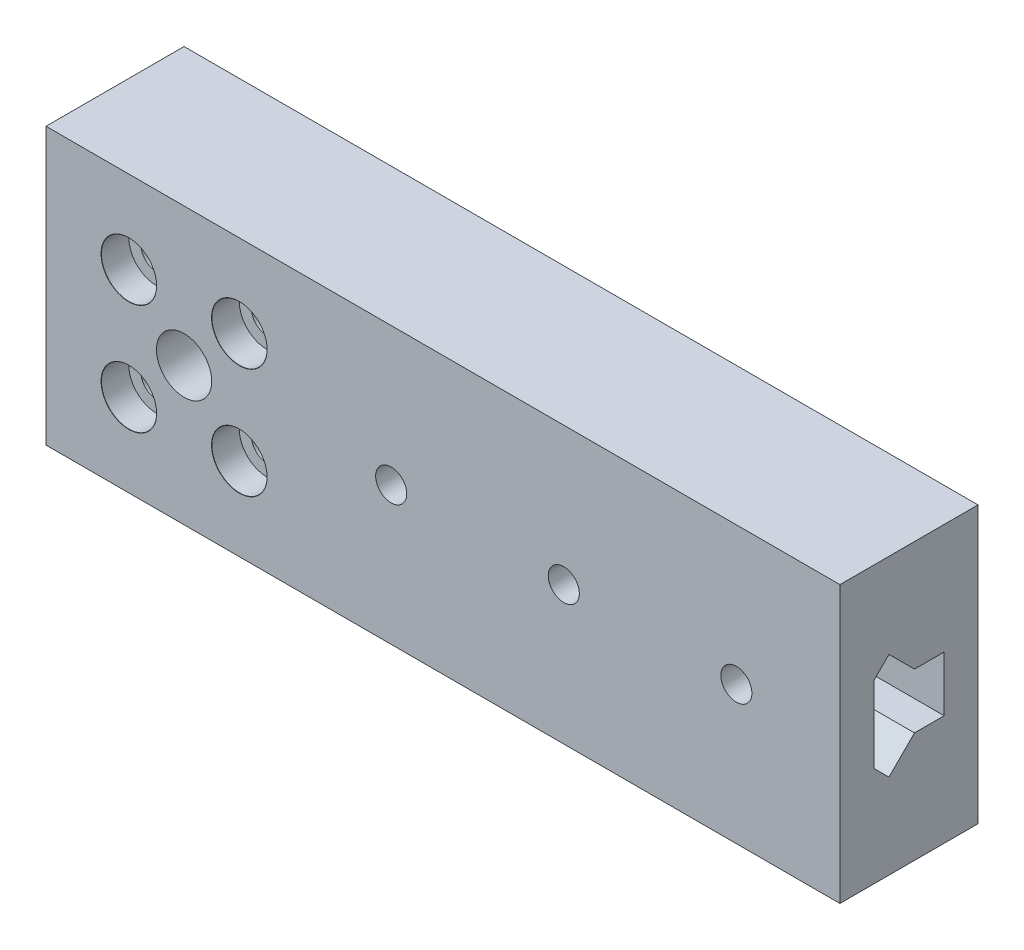
SolidWorks part; units mm, degrees
ref_plane "Front Plane" through (0, 0, 0) normal (0, 0, 1) x (1, 0, 0)
ref_plane "Top Plane" through (0, 0, 0) normal (0, 1, 0) x (1, 0, 0)
ref_plane "Right Plane" through (0, 0, 0) normal (1, 0, 0) x (0, 0, -1)
sketch "Sketch1" plane through (0, 0, 0) normal (0, 0, 1) x (1, 0, 0)
  line L0 (-40, 20) -> (-40, -20)
  line L1 (-40, -20) -> (75, -20)
  line L2 (75, -20) -> (75, 20)
  line L3 (75, 20) -> (-40, 20)
  circle A0 centre (-20, 0) radius 4
  point P5 (0, 0)
  point P6 (-40, 0)
  point P9 (0, 0)
  dimension "D2" = 8
  dimension "D1" = 40
  dimension "D3" = 40
  dimension "D4" = 20
  dimension "D5" = 75
extrude "Boss-Extrude1" add sketch "Sketch1" along normal mid plane 20
hole_wizard "CBORE for M4 SHCS1" positions "Sketch4" profile "Sketch3" counterbore size "M4" standard "ANSI Metric" end condition through all
sketch "Sketch4" plane through (0, 0, 10) normal (0, 0, 1) x (1, 0, 0)
  line L1 (-28, -8) -> (-12, -8)
  line L2 (-28, -8) -> (-28, 8)
  line L3 (-28, 8) -> (-12, 8)
  line L4 (-12, -8) -> (-12, 8)
  line L5 (-28, -8) -> (-12, 8) construction
  line L6 (-28, 8) -> (-12, -8) construction
  circle A0 centre (-20, 0) radius 4 construction
  circle A1 centre (-20, 0) radius 4
  point P0 (-28, 8)
  point P5 (-12, 8)
  point P68 (-28, -8)
  point P70 (-12, -8)
  dimension "D1" = 16
sketch "Sketch3" plane through (-28, 8, 10) normal (1, 0, 0) x (0, -1, 0)
  line L0 (0, 0) -> (0, 20)
  line L1 (0, 20) -> (2.25, 20)
  line L3 (2.25, 20) -> (2.25, 4)
  line L4 (4, 4) -> (2.25, 4)
  line L5 (4, 4) -> (4, 0.025)
  line L6 (4, 0.025) -> (4.025, 0)
  line L7 (4.025, 0) -> (0, 0)
  line L8 (-4, 0.025) -> (-4.025, 0) construction
  line L11 (0, -6.35) -> (0, 107.95) construction
  dimension "Thru Hole Dia." = 4.5
  dimension "Thru Hole Depth" = 20
  dimension "C'Bore Dia." = 8
  dimension "C'Bore Depth" = 4
  dimension "Near C'Sink Dia." = 8.05
  dimension "Near C'Sink Angle" = 90
sketch "Sketch5" plane through (0, 0, -10) normal (0, 0, -1) x (-1, 0, 0)
  circle A0 centre (20, 0) radius 16.5
  circle A1 centre (20, 0) radius 4 construction
  circle A2 centre (20, 0) radius 4
  point P5 (20, -0.3706)
  dimension "D1" = 33
extrude "Cut-Extrude1" cut sketch "Sketch5" against normal offset from surface (12 mm away) 8 up to face at (-23.975, 8, 10)
sketch "Sketch6" plane through (75, 0, 0) normal (1, 0, 0) x (0, 0, -1)
  line L1 (-5.1, 5.5) -> (-2.9, 7.7)
  line L2 (-2.9, 7.7) -> (0.8, 4)
  line L3 (0.8, 4) -> (5.1, 4)
  line L9 (-5.1, 0) -> (-5.1, 5.5)
  line L10 (5.1, 4) -> (5.1, 0)
  line L11 (-5.1, 0) -> (5.1, 0)
  point P1 (0, 0)
  point P6 (-4.6748, 0)
  point P8 (-1.1673, 7.5903)
  point P9 (-1.2573, 6.4511)
  point P10 (-1.1973, 8.1898)
  point P11 (-3.0993, 0)
  point P12 (1.0014, 4)
  point P13 (-2.8475, 7.7)
  dimension "D1" = 135
  dimension "D2" = 8
  dimension "D3" = 4
  dimension "D4" = 5.5
  dimension "D5" = 10.2
extrude "Cut-Extrude2" cut sketch "Sketch6" against normal up to surface (75 mm away) up to plane "Right Plane"
mirror "Mirror1" about plane through (-12.7801, 0, 5.1) normal (0, -1, 0) of "Cut-Extrude2"
hole_wizard "M4 Clearance Hole1" positions "Sketch7" profile "Sketch8" hole size "M4" standard "ANSI Metric" end condition through all
sketch "Sketch7" plane through (0, 0, -10) normal (0, 0, -1) x (-1, 0, 0)
  line L0 (-60, 0) -> (-10, 0)
  point P0 (-10, 0)
  point P2 (-35, 0)
  point P5 (-60, 0)
  point P12 (0, 0)
  dimension "D1" = 50
  dimension "D2" = 10
sketch "Sketch8" plane through (10, 0, -10) normal (1, 0, 0) x (0, 1, 0)
  line L0 (0, 0) -> (0, 20)
  line L1 (0, 20) -> (2.25, 20)
  line L2 (2.25, 20) -> (2.25, 0)
  line L5 (2.25, 0) -> (0, 0)
  line L11 (0, -6.35) -> (0, 107.95) construction
  dimension "Thru Hole Dia." = 4.5
  dimension "Thru Hole Depth" = 20
